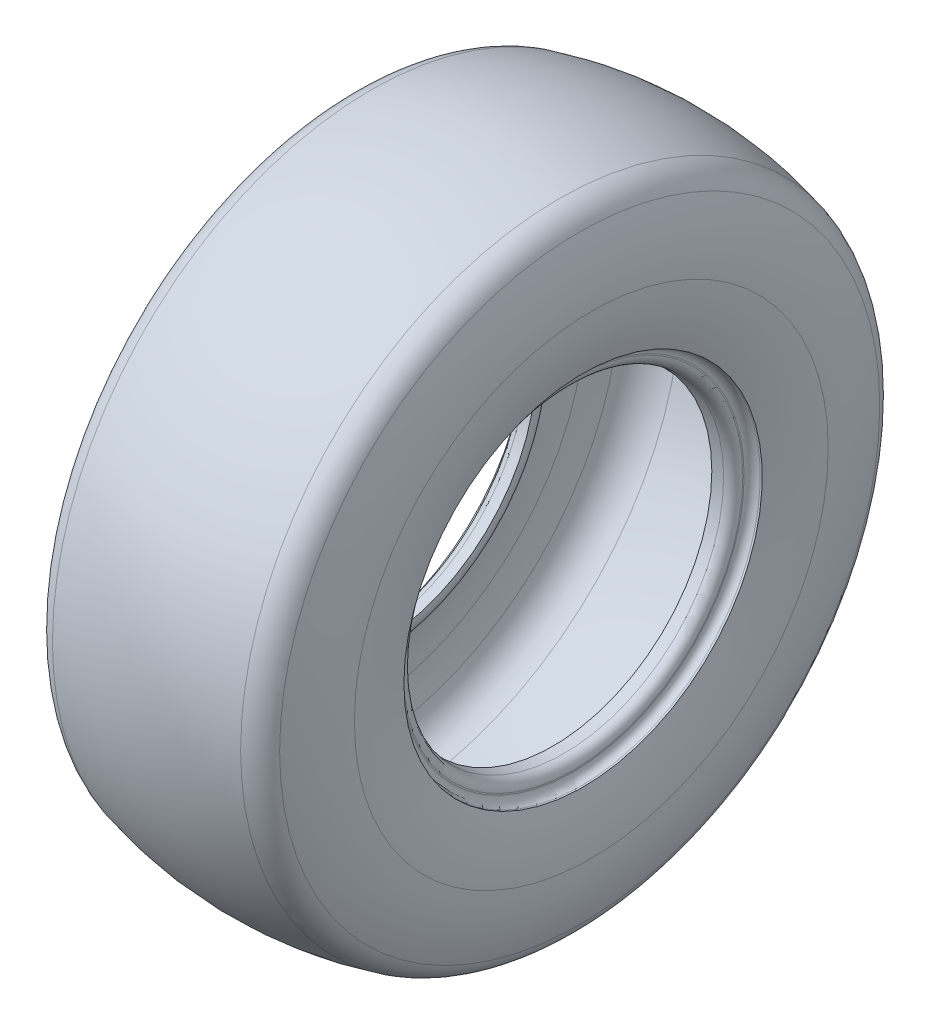
SolidWorks part; units mm, degrees
material "Rubber"
ref_plane "Front Plane" through (0, 0, 0) normal (0, 0, 1) x (1, 0, 0)
ref_plane "Top Plane" through (0, 0, 0) normal (0, 1, 0) x (1, 0, 0)
ref_plane "Right Plane" through (0, 0, 0) normal (1, 0, 0) x (0, 0, -1)
other "WHEEL-WIDTH"
ref_axis "Axis1" through (-88.99, 0, 0) along (1, 0, 0)
sketch "Def-Points" plane through (0, 0, 0) normal (0, 0, 1) x (1, 0, 0)
  line L0 (0, 209.042) -> (0, 0) construction
  line L1 (0, -114.9731) -> (0, 114.9731) construction
  line L2 (-68.326, 101.6) -> (68.326, 101.6) construction
  line L3 (-12.4058, 0) -> (13.7176, 0) construction
  line L4 (254.2457, 0) -> (-254.2457, 0) construction
  line L5 (-231.1324, 0) -> (231.1324, 0) construction
  line L6 (-62.5294, 101.0929) -> (-55.626, 100.4889)
  line L7 (-68.326, 107.4187) -> (-68.326, 108.2548)
  line L8 (-79.883, 149.86) -> (79.883, 149.86) construction
  line L9 (-68.58, 198.882) -> (68.58, 198.882) construction
  line L10 (-74.676, 113.3348) -> (-73.406, 113.3348)
  line L11 (74.676, 113.3348) -> (73.406, 113.3348)
  line L12 (68.326, 107.4187) -> (68.326, 108.2548)
  line L13 (62.5294, 101.0929) -> (55.626, 100.4889)
  arc A0 (-68.326, 108.2548) -> (-73.406, 113.3348) centre (-73.406, 108.2548) ccw
  arc A1 (-62.5294, 101.0929) -> (-68.326, 107.4187) centre (-61.976, 107.4187) cw
  arc A2 (62.5294, 101.0929) -> (68.326, 107.4187) centre (61.976, 107.4187) ccw
  arc A3 (68.326, 108.2548) -> (73.406, 113.3348) centre (73.406, 108.2548) cw
  point P8 (-68.326, 101.6)
  point P9 (68.326, 101.6)
  dimension "D6" = 5.08
  dimension "D2" = 6.35
  dimension "RIM_WIDTH" = 136.652
  dimension "RIM_TAPER" = 5
  dimension "BEAD_WIDTH" = 12.7
  dimension "MOLDED_SW" = 159.766
  dimension "CL-SEC-HGT" = 48.26
  dimension "FLANGE-WIDTH" = 6.35
  dimension "FLANGE_HEIGHT" = 11.7348
  dimension "TAW" = 137.16
  dimension "SHOULDER_DROP" = 10.16
  dimension "HALF-RIM-DIA" = 101.6
  dimension "TIRE-DIA" = 418.084
sketch "Outer-Profile" plane through (0, 0, 0) normal (0, 0, 1) x (1, 0, 0)
  line L1 (-79.883, 149.86) -> (79.883, 149.86) construction
  line L2 (0, 209.042) -> (0, 0) construction
  arc A0 (-74.676, 113.3348) -> (-79.883, 149.86) centre (50.826, 149.86) cw
  arc A1 (-72.5208, 189.7888) -> (-79.883, 149.86) centre (32.0746, 149.86) ccw
  arc A2 (74.676, 113.3348) -> (79.883, 149.86) centre (-50.826, 149.86) ccw
  arc A3 (72.5208, 189.7888) -> (79.883, 149.86) centre (-32.0746, 149.86) cw
  arc A4 (-59.5168, 201.4319) -> (59.5168, 201.4319) centre (0, -27.4955) cw
  arc A5 (72.5208, 189.7888) -> (59.5168, 201.4319) centre (54.7235, 182.9948) ccw
  arc A6 (-59.5168, 201.4319) -> (-72.5208, 189.7888) centre (-54.7235, 182.9948) ccw
  point P22 (68.58, 198.882)
  point P25 (-68.58, 198.882)
  dimension "SHOULDER-RADIUS" = 19.05
sketch "Carcass-Sketch1" plane through (0, 0, 0) normal (0, 0, 1) x (1, 0, 0)
  line L0 (62.5294, 101.0929) -> (55.626, 100.4889) construction
  line L1 (68.326, 107.4187) -> (68.326, 108.2548) construction
  line L2 (74.676, 113.3348) -> (73.406, 113.3348) construction
  line L3 (-62.5294, 101.0929) -> (-55.626, 100.4889) construction
  line L4 (-68.326, 107.4187) -> (-68.326, 108.2548) construction
  line L5 (-74.676, 113.3348) -> (-73.406, 113.3348) construction
  line L6 (62.5294, 101.0929) -> (55.626, 100.4889)
  line L7 (68.326, 107.4187) -> (68.326, 108.2548)
  line L8 (74.676, 113.3348) -> (73.406, 113.3348)
  line L9 (-62.5294, 101.0929) -> (-55.626, 100.4889)
  line L10 (-68.326, 107.4187) -> (-68.326, 108.2548)
  line L11 (-74.676, 113.3348) -> (-73.406, 113.3348)
  arc A0 (71.6746, 169.5846) -> (52.7173, 189.5228) centre (46.7216, 164.8406) ccw
  arc A1 (52.7173, 189.5228) -> (-52.7173, 189.5228) centre (0, -27.4955) ccw
  arc A2 (57.7912, 194.7945) -> (-57.7912, 194.7945) centre (0, -27.4955) ccw
  arc A3 (57.7912, 194.7945) -> (-57.7912, 194.7945) centre (0, -27.4955) ccw construction
  arc A4 (-52.7173, 189.5228) -> (-71.6746, 169.5846) centre (-46.7216, 164.8406) ccw
  arc A5 (-55.626, 100.4889) -> (-61.9506, 112.6399) centre (-68.326, 101.6) ccw
  arc A6 (61.9506, 112.6399) -> (55.626, 100.4889) centre (68.326, 101.6) ccw
  arc A7 (-71.1013, 125.3879) -> (-61.9506, 112.6399) centre (-52.4238, 129.1366) ccw
  arc A8 (-66.5884, 187.5241) -> (-73.533, 149.86) centre (32.0746, 149.86) ccw
  arc A9 (-73.533, 149.86) -> (-68.579, 115.1092) centre (50.826, 149.86) ccw
  arc A10 (-71.6746, 169.5846) -> (-73.533, 149.86) centre (32.0746, 149.86) ccw
  arc A11 (-73.533, 149.86) -> (-71.1013, 125.3879) centre (50.826, 149.86) ccw
  arc A12 (56.1934, 188.6488) -> (-56.1934, 188.6488) centre (0, -27.4955) ccw construction
  arc A14 (73.533, 149.86) -> (66.5884, 187.5241) centre (-32.0746, 149.86) ccw
  arc A15 (68.579, 115.1092) -> (73.533, 149.86) centre (-50.826, 149.86) ccw
  arc A16 (73.533, 149.86) -> (71.6746, 169.5846) centre (-32.0746, 149.86) ccw
  arc A23 (-79.883, 149.86) -> (-74.676, 113.3348) centre (50.826, 149.86) ccw construction
  arc A24 (-72.5208, 189.7888) -> (-79.883, 149.86) centre (32.0746, 149.86) ccw construction
  arc A25 (-59.5168, 201.4319) -> (-72.5208, 189.7888) centre (-54.7235, 182.9948) ccw construction
  arc A26 (59.5168, 201.4319) -> (-59.5168, 201.4319) centre (0, -27.4955) ccw construction
  arc A27 (72.5208, 189.7888) -> (59.5168, 201.4319) centre (54.7235, 182.9948) ccw construction
  arc A28 (79.883, 149.86) -> (72.5208, 189.7888) centre (-32.0746, 149.86) ccw construction
  arc A29 (74.676, 113.3348) -> (79.883, 149.86) centre (-50.826, 149.86) ccw construction
  arc A30 (-79.883, 149.86) -> (-74.676, 113.3348) centre (50.826, 149.86) ccw
  arc A31 (-72.5208, 189.7888) -> (-79.883, 149.86) centre (32.0746, 149.86) ccw
  arc A32 (-59.5168, 201.4319) -> (-72.5208, 189.7888) centre (-54.7235, 182.9948) ccw
  arc A33 (59.5168, 201.4319) -> (-59.5168, 201.4319) centre (0, -27.4955) ccw
  arc A34 (72.5208, 189.7888) -> (59.5168, 201.4319) centre (54.7235, 182.9948) ccw
  arc A35 (79.883, 149.86) -> (72.5208, 189.7888) centre (-32.0746, 149.86) ccw
  arc A36 (74.676, 113.3348) -> (79.883, 149.86) centre (-50.826, 149.86) ccw
  arc A37 (73.406, 113.3348) -> (68.326, 108.2548) centre (73.406, 108.2548) ccw construction
  arc A38 (62.5294, 101.0929) -> (68.326, 107.4187) centre (61.976, 107.4187) ccw construction
  arc A39 (-68.326, 108.2548) -> (-73.406, 113.3348) centre (-73.406, 108.2548) ccw construction
  arc A40 (-68.326, 107.4187) -> (-62.5294, 101.0929) centre (-61.976, 107.4187) ccw construction
  arc A41 (73.406, 113.3348) -> (68.326, 108.2548) centre (73.406, 108.2548) ccw
  arc A42 (62.5294, 101.0929) -> (68.326, 107.4187) centre (61.976, 107.4187) ccw
  arc A43 (-68.326, 108.2548) -> (-73.406, 113.3348) centre (-73.406, 108.2548) ccw
  arc A44 (-68.326, 107.4187) -> (-62.5294, 101.0929) centre (-61.976, 107.4187) ccw
  arc A45 (61.9506, 112.6399) -> (71.1013, 125.3879) centre (52.4238, 129.1366) ccw
  arc A46 (71.1013, 125.3879) -> (73.533, 149.86) centre (-50.826, 149.86) ccw
  dimension "D5" = 25.4
  dimension "D6" = 19.05
  dimension "D1" = 6.858
  dimension "D2" = 6.35
  dimension "D3" = 6.35
  dimension "D4" = 6.35
revolve "Revolve1" add sketch "Carcass-Sketch1" angle 360 about axis through (-88.99, 0, 0) along (1, 0, 0)
equation "\"D6@Def-Points\" = \"FLANGE-WIDTH@Def-Points\" - .05"
